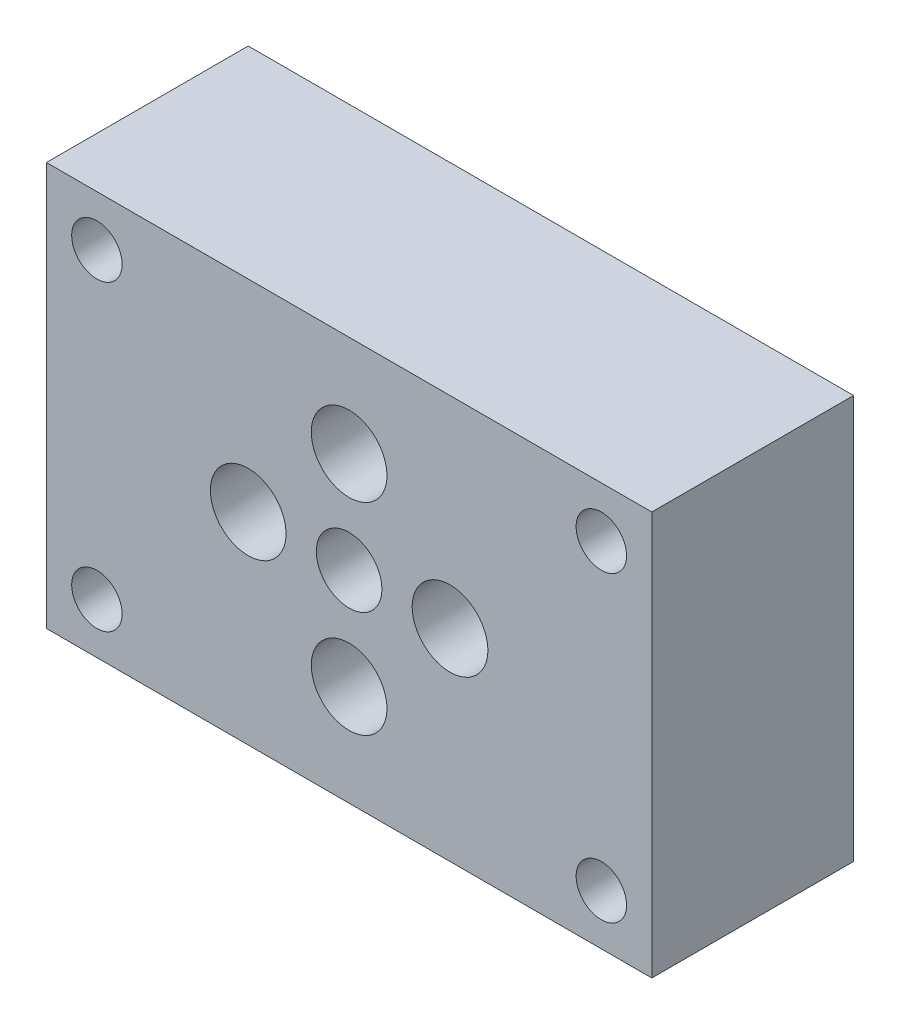
SolidWorks part; units mm, degrees
ref_plane "前视基准面" through (0, 0, 0) normal (0, 0, 1) x (1, 0, 0)
ref_plane "上视基准面" through (0, 0, 0) normal (0, 1, 0) x (1, 0, 0)
ref_plane "右视基准面" through (0, 0, 0) normal (1, 0, 0) x (0, 0, -1)
sketch "草图1" plane through (0, 0, 0) normal (0, 0, 1) x (1, 0, 0)
  line L1 (38.1, -25.4) -> (-38.1, -25.4)
  line L2 (38.1, -25.4) -> (38.1, 25.4)
  line L3 (38.1, 25.4) -> (-38.1, 25.4)
  line L4 (-38.1, -25.4) -> (-38.1, 25.4)
  line L5 (38.1, -25.4) -> (-38.1, 25.4) construction
  line L6 (38.1, 25.4) -> (-38.1, -25.4) construction
  point P0 (0, 0)
  dimension "D1" = 76.2
  dimension "D2" = 50.8
extrude "凸台-拉伸1" add sketch "草图1" against normal blind 25.4
sketch "草图2" plane through (0, 0, 0) normal (0, 0, 1) x (1, 0, 0)
  circle A0 centre (0, 0) radius 4.1275
extrude "切除-拉伸1" cut sketch "草图2" against normal blind 25.4
sketch "草图3" plane through (0, 0, -25.4) normal (0, 0, -1) x (-1, 0, 0)
  line L0 (-38.1, -25.4) -> (-38.1, 25.4) construction
  line L3 (-38.1, 25.4) -> (38.1, 25.4) construction
  circle A0 centre (-31.75, 19.05) radius 3.175
  circle A1 centre (31.75, 19.05) radius 3.175
  dimension "D3" = 6.35
  dimension "D1" = 6.35
  dimension "D2" = 6.35
  dimension "D4" = 2
extrude "切除-拉伸2" cut sketch "草图3" against normal through all
sketch "草图4" plane through (0, 0, -25.4) normal (0, 0, -1) x (-1, 0, 0)
  line L0 (-38.1, -25.4) -> (-38.1, 25.4) construction
  line L1 (38.1, -25.4) -> (-38.1, -25.4) construction
  circle A0 centre (-31.75, -19.05) radius 3.175
  circle A1 centre (31.75, -19.05) radius 3.175
  dimension "D3" = 2
  dimension "D1" = 6.35
  dimension "D2" = 6.35
extrude "切除-拉伸3" cut sketch "草图4" against normal blind 25.4
sketch "草图5" plane through (0, 0, -25.4) normal (0, 0, -1) x (-1, 0, 0)
  circle A0 centre (0, 12.7) radius 4.7625
  circle A1 centre (0, -12.7) radius 4.7625
  dimension "D1" = 12.7
  dimension "D2" = 2
extrude "切除-拉伸4" cut sketch "草图5" against normal blind 25.4
sketch "草图6" plane through (0, 0, -25.4) normal (0, 0, -1) x (-1, 0, 0)
  circle A0 centre (-12.7, 0) radius 4.7625
  circle A1 centre (12.7, 0) radius 4.7625
  point P2 (0, 0)
  point P4 (0, 0)
  dimension "D1" = 12.7
  dimension "D2" = 2
extrude "切除-拉伸5" cut sketch "草图6" against normal blind 25.4
